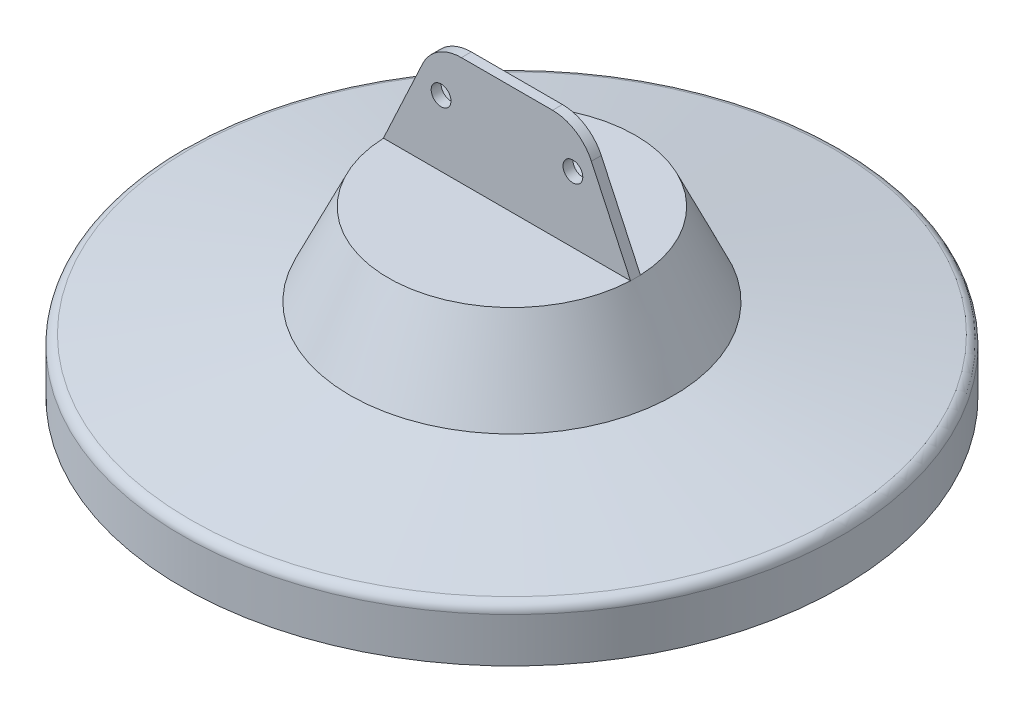
SolidWorks part; units mm, degrees
ref_plane "Front Plane" through (0, 0, 0) normal (0, 0, 1) x (1, 0, 0)
ref_plane "Top Plane" through (0, 0, 0) normal (0, 1, 0) x (1, 0, 0)
ref_plane "Right Plane" through (0, 0, 0) normal (1, 0, 0) x (0, 0, -1)
sketch "Sketch1" plane through (0, 0, 0) normal (0, 0, 1) x (1, 0, 0)
  line L0 (0, 0) -> (0, 50) construction
  line L1 (0, 0) -> (-100, 0)
  line L2 (-100, 0) -> (-100, 13.5178)
  line L3 (-97.5209, 16.4723) -> (-49.1577, 25)
  line L4 (-49.1577, 25) -> (-37.5, 50)
  line L5 (-37.5, 50) -> (0, 50)
  line L6 (0, 50) -> (0, 0)
  arc A0 (-100, 13.5178) -> (-97.5209, 16.4723) centre (-97, 13.5178) cw
  dimension "D2" = 100
  dimension "D3" = 10
  dimension "D5" = 3
  dimension "D1" = 50
  dimension "D4" = 37.5
  dimension "D6" = 25
  dimension "D7" = 25
revolve "Revolve1" add sketch "Sketch1" angle 360 about L0
sketch "Sketch2" plane through (0, 0, 0) normal (0, 0, 1) x (1, 0, 0)
  line L0 (-37.5, 50) -> (-25.6119, 75.494)
  line L1 (-13.8299, 83) -> (13.8299, 83)
  line L2 (25.6119, 75.494) -> (37.5, 50)
  line L3 (-100, 0) -> (100, 0) construction
  line L4 (-20, 70) -> (20, 70) construction
  line L5 (20, 70) -> (0, 70) construction
  line L6 (-37.5, 50) -> (-49.1577, 25) construction
  line L7 (49.1577, 25) -> (37.5, 50) construction
  line L8 (0, 70) -> (0, 0) construction
  line L9 (-37.5, 50) -> (37.5, 50)
  circle A0 centre (-20, 70) radius 3
  circle A1 centre (20, 70) radius 3
  arc A2 (13.8299, 83) -> (25.6119, 75.494) centre (13.8299, 70) cw
  arc A3 (-25.6119, 75.494) -> (-13.8299, 83) centre (-13.8299, 70) cw
  dimension "D2" = 6
  dimension "D4" = 13
  dimension "D1" = 83
  dimension "D3" = 40
  dimension "D5" = 70
extrude "Boss-Extrude1" add sketch "Sketch2" along normal mid plane 3
